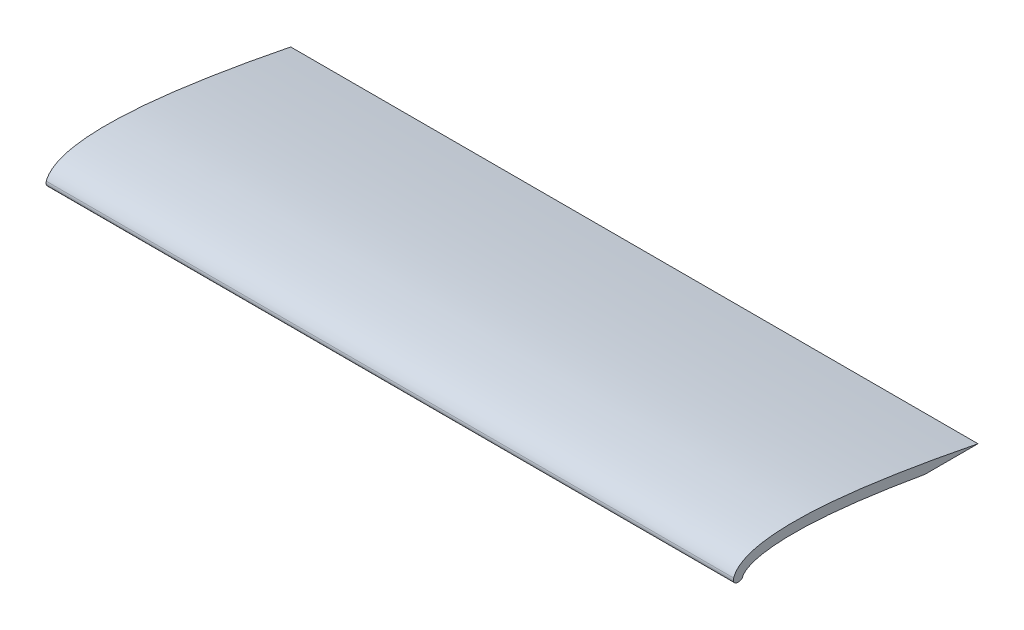
SolidWorks part; units mm, degrees
material "PS HI"
ref_plane "Front Plane" through (0, 0, 0) normal (0, 0, 1) x (1, 0, 0)
ref_plane "Top Plane" through (0, 0, 0) normal (0, 1, 0) x (1, 0, 0)
ref_plane "Right Plane" through (0, 0, 0) normal (1, 0, 0) x (0, 0, -1)
sketch "Sketch1" plane through (0, 0, 0) normal (1, 0, 0) x (0, 0, -1)
  line L0 (0, 0) -> (63.5, 0)
  line L1 (0, 0) -> (0, 12.7) construction
  line L2 (0, 12.7) -> (63.5, 0) construction
  spline S0 degree 2 poles (0, 0) (0, 12.7) (63.5, 0) knots 0 0 0 1 1 1
  spline S1 degree 1 poles (2.54, 0) (63.0019, -2.4907) knots 0 0 1 1 construction
  spline S2 degree 2 poles (2.54, 0) (2.5435, 0.292) (2.6529, 0.7053) (2.8937, 1.1372) (3.567, 1.7498) (4.8349, 2.4132) (6.7202, 3.0045) (9.8145, 3.5703) (15.6113, 3.9063) (24.3458, 3.5199) (43.22, 1.4623) (63.0019, -2.4907) knots 0 0 0 0.046875 0.09375 0.15625 0.21875 0.28125 0.34375 0.4375 0.5625 0.6875 1 1 1
  dimension "D1" = 63.5
  dimension "D2" = 12.7
  dimension "D3" = 2.54
extrude "Boss-Extrude1" add sketch "Sketch1" along normal blind 177.8 contours L0 S2 S0
fillet "Fillet1" radius 1.143 2 edges at (88.9, 0, -2.54) (88.9, 0, 0)
